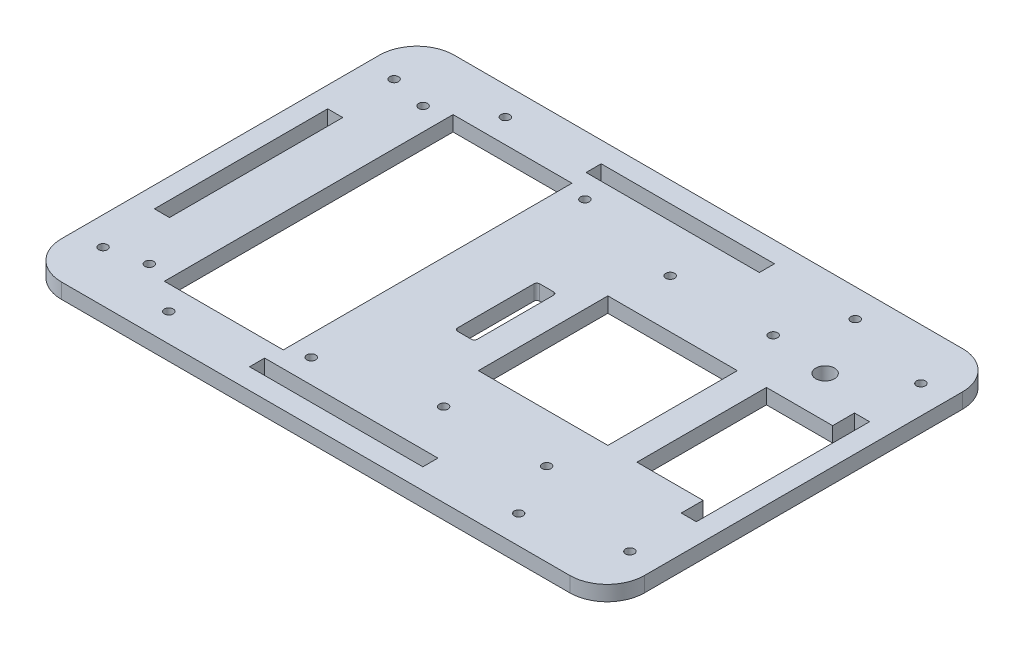
SolidWorks part; units mm, degrees
ref_plane "Front Plane" through (0, 0, 0) normal (0, 0, 1) x (1, 0, 0)
ref_plane "Top Plane" through (0, 0, 0) normal (0, 1, 0) x (1, 0, 0)
ref_plane "Right Plane" through (0, 0, 0) normal (1, 0, 0) x (0, 0, -1)
sketch "Sketch1" plane through (0, 0, 0) normal (0, 1, 0) x (1, 0, 0)
  line L1 (-55.2072, 101.2499) -> (117.5428, 101.2499)
  line L2 (-67.9072, 88.5499) -> (-67.9072, -19.5301)
  line L3 (-55.2072, -32.2301) -> (117.5428, -32.2301)
  line L4 (130.2428, 88.5499) -> (130.2428, -19.5301)
  arc A0 (-55.2072, -32.2301) -> (-67.9072, -19.5301) centre (-55.2072, -19.5301) cw
  arc A1 (-55.2072, 101.2499) -> (-67.9072, 88.5499) centre (-55.2072, 88.5499) ccw
  arc A2 (117.5428, 101.2499) -> (130.2428, 88.5499) centre (117.5428, 88.5499) cw
  arc A3 (130.2428, -19.5301) -> (117.5428, -32.2301) centre (117.5428, -19.5301) cw
  point P6 (-67.9072, -32.2301)
  point P9 (-67.9072, 101.2499)
  point P14 (130.2428, -32.2301)
  dimension "D3" = 12.7
  dimension "D4" = 12.7
  dimension "D5" = 12.7
  dimension "D1" = 133.48
  dimension "D2" = 198.15
extrude "Main" add sketch "Sketch1" along normal blind 5.13
sketch "Sketch2" plane through (0, 5.13, 0) normal (0, 1, 0) x (1, 0, 0)
  line L0 (117.5428, 101.2499) -> (-55.2072, 101.2499) construction
  line L1 (-60.9072, 63.9499) -> (-55.7772, 63.9499)
  line L2 (-60.9072, 63.9499) -> (-60.9072, 5.0699)
  line L3 (-60.9072, 5.0699) -> (-55.7772, 5.0699)
  line L4 (-55.7772, 63.9499) -> (-55.7772, 5.0699)
  line L5 (31.1678, 101.2499) -> (31.1678, -32.2301) construction
  line L6 (-55.2072, -32.2301) -> (117.5428, -32.2301) construction
  line L7 (130.2428, 34.5099) -> (-67.9072, 34.5099) construction
  line L8 (130.2428, -19.5301) -> (130.2428, 88.5499) construction
  line L9 (1.7278, 94.2499) -> (60.6078, 94.2499)
  line L10 (1.7278, 94.2499) -> (1.7278, 89.1199)
  line L11 (1.7278, 89.1199) -> (60.6078, 89.1199)
  line L12 (60.6078, 94.2499) -> (60.6078, 89.1199)
  line L13 (123.2428, 63.9499) -> (118.1128, 63.9499)
  line L14 (123.2428, 63.9499) -> (123.2428, 5.0699)
  line L15 (118.1128, 63.9499) -> (118.1128, 5.0699)
  line L16 (123.2428, 5.0699) -> (118.1128, 5.0699)
  line L17 (-67.9072, 88.5499) -> (-67.9072, -19.5301) construction
  line L18 (60.6078, -25.2301) -> (60.6078, -20.1001)
  line L19 (1.7278, -25.2301) -> (1.7278, -20.1001)
  line L20 (1.7278, -25.2301) -> (60.6078, -25.2301)
  line L21 (1.7278, -20.1001) -> (60.6078, -20.1001)
  line L23 (-67.9072, 88.5499) -> (-67.9072, -19.5301) construction
  circle A0 centre (-28.2722, 91.6899) radius 1.5
  circle A1 centre (90.6078, 91.6899) radius 1.5
  circle A2 centre (-58.3472, -14.9301) radius 1.5
  circle A3 centre (-58.3472, 83.9499) radius 1.5
  circle A4 centre (120.6828, 83.9499) radius 1.5
  circle A5 centre (120.6828, -14.9301) radius 1.5
  circle A6 centre (90.6078, -22.6701) radius 1.5
  circle A7 centre (-28.2722, -22.6701) radius 1.5
  point P44 (31.1678, 94.2499)
  dimension "D13" = 3
  dimension "D14" = 3
  dimension "D15" = 3
  dimension "D16" = 3
  dimension "D1" = 58.88
  dimension "D2" = 5.13
  dimension "D3" = 7
  dimension "D4" = 5.13
  dimension "D5" = 37.3
  dimension "D6" = 99.075
  dimension "D7" = 58.88
  dimension "D8" = 7
  dimension "D9" = 30
  dimension "D10" = 20
  dimension "D11" = 20
  dimension "D12" = 30
  dimension "D17" = 9.56
  dimension "D18" = 9.56
  dimension "D19" = 9.56
  dimension "D20" = 9.56
extrude "Assembly slots" cut sketch "Sketch2" against normal up to next
sketch "Sketch3" plane through (0, 0, 0) normal (0, -1, 0) x (1, 0, 0)
  line L0 (117.5428, -101.2499) -> (-55.2072, -101.2499) construction
  line L1 (-37.9072, 14.5401) -> (2.4928, 14.5401)
  line L2 (-37.9072, 14.5401) -> (-37.9072, -83.5599)
  line L3 (-37.9072, -83.5599) -> (2.4928, -83.5599)
  line L4 (2.4928, 14.5401) -> (2.4928, -83.5599)
  line L5 (-67.9072, -88.5499) -> (-67.9072, 19.5301) construction
  line L6 (130.2428, 19.5301) -> (130.2428, -88.5499) construction
  line L7 (41.7428, -12.5099) -> (85.7428, -12.5099)
  line L8 (41.7428, -12.5099) -> (41.7428, -56.5099)
  line L9 (41.7428, -56.5099) -> (85.7428, -56.5099)
  line L10 (85.7428, -12.5099) -> (85.7428, -56.5099)
  dimension "D1" = 40.4
  dimension "D2" = 98.1
  dimension "D3" = 17.69
  dimension "D4" = 30
  dimension "D5" = 44
  dimension "D6" = 44
  dimension "D7" = 44.5
  dimension "D8" = 44.74
extrude "LCD and Block slot" cut sketch "Sketch3" against normal up to next
ref_plane "Plane1" through (-55.2072, 0, -101.2499) normal (-1, 0, 0) x (0, 0, 1)
hole_wizard "LCD screwholes" positions "Sketch7" profile "Sketch6" hole size "Ø3.0" standard "Ansi Metric"
sketch "Sketch7" plane through (0, 5.13, 0) normal (0, 1, 0) x (-1, 0, 0)
  line L0 (55.2072, 32.2301) -> (-117.5428, 32.2301) construction
  point P3 (45.5572, 11.9901)
  point P30 (-9.4428, 11.9901)
  point P31 (45.5572, -81.0099)
  point P32 (-9.4428, -81.0099)
  dimension "D1" = 2
  dimension "D3" = 93
  dimension "D4" = 20.24
  dimension "D2" = 2
sketch "Sketch6" plane through (-45.5572, 5.13, 11.9901) normal (1, 0, 0) x (0, 0, 1)
  line L0 (0, 0) -> (0, 26.3013)
  line L1 (0, 26.3013) -> (1.5, 25.4)
  line L2 (1.5, 25.4) -> (1.5, 0)
  line L5 (1.5, 0) -> (0, 0)
  line L10 (0, 26.3013) -> (-1.5, 25.4) construction
  line L11 (0, -6.35) -> (0, 107.95) construction
  dimension "Hole Dia." = 3
  dimension "Hole Depth" = 25.4
  dimension "Drill Angle" = 118
hole_wizard "Core screwholes" positions "Sketch9" profile "Sketch8" hole size "Ø3.0" standard "Ansi Metric"
sketch "Sketch9" plane through (0, 5.13, 0) normal (0, 1, 0) x (-1, 0, 0)
  line L0 (-117.5428, -101.2499) -> (55.2072, -101.2499) construction
  point P1 (-46.4274, -73.0099)
  dimension "D2" = 28.24
sketch "Sketch8" plane through (46.4274, 5.13, -73.0099) normal (1, 0, 0) x (0, 0, 1)
  line L0 (0, 0) -> (0, 26.3013)
  line L1 (0, 26.3013) -> (1.5, 25.4)
  line L2 (1.5, 25.4) -> (1.5, 0)
  line L5 (1.5, 0) -> (0, 0)
  line L10 (0, 26.3013) -> (-1.5, 25.4) construction
  line L11 (0, -6.35) -> (0, 107.95) construction
  dimension "Hole Dia." = 3
  dimension "Hole Depth" = 25.4
  dimension "Drill Angle" = 118
pattern_linear "Core screwholes pattern" count 2 spacing 35 along (1, 0, 0) count 2 spacing 77 along (0, 0, 1) of "Core screwholes"
sketch "Sketch11" plane through (0, 5.13, 0) normal (0, 1, 0) x (1, 0, 0)
  line L0 (117.5428, 101.2499) -> (-55.2072, 101.2499) construction
  line L1 (95.6244, 12.5099) -> (118.1244, 12.5099)
  line L2 (95.6244, 12.5099) -> (95.6244, 56.5099)
  line L3 (95.6244, 56.5099) -> (118.1244, 56.5099)
  line L4 (118.1244, 12.5099) -> (118.1244, 56.5099)
  dimension "D1" = 22.5
  dimension "D2" = 44
  dimension "D3" = 44.74
extrude "Hinge slot" cut sketch "Sketch11" against normal up to next
sketch "Sketch13" plane through (0, 5.13, 0) normal (0, 1, 0) x (1, 0, 0)
  line L1 (26.6266, 48.4799) -> (31.3266, 48.4799)
  line L2 (25.6266, 47.4799) -> (25.6266, 21.5399)
  line L3 (26.6266, 20.5399) -> (31.3266, 20.5399)
  line L4 (32.3266, 47.4799) -> (32.3266, 21.5399)
  line L5 (117.5428, 101.2499) -> (-55.2072, 101.2499) construction
  arc A0 (26.6266, 20.5399) -> (25.6266, 21.5399) centre (26.6266, 21.5399) cw
  arc A1 (32.3266, 21.5399) -> (31.3266, 20.5399) centre (31.3266, 21.5399) cw
  arc A2 (31.3266, 48.4799) -> (32.3266, 47.4799) centre (31.3266, 47.4799) cw
  arc A3 (26.6266, 48.4799) -> (25.6266, 47.4799) centre (26.6266, 47.4799) ccw
  point P10 (25.6266, 20.5399)
  point P17 (25.6266, 48.4799)
  dimension "D3" = 1
  dimension "D1" = 27.94
  dimension "D2" = 52.77
  dimension "D4" = 6.7
extrude "Latch Slot" cut sketch "Sketch13" against normal up to next
hole_wizard "Lid thermistor hole" positions "Sketch15" profile "Sketch14" hole size "#6" standard "Ansi Inch"
sketch "Sketch15" plane through (0, 5.13, 0) normal (0, 1, 0) x (-1, 0, 0)
  point P0 (-101.4724, -70.6026)
sketch "Sketch14" plane through (101.4724, 5.13, -70.6026) normal (1, 0, 0) x (0, 0, 1)
  line L0 (0, 0) -> (0, 9.5077)
  line L1 (0, 9.5077) -> (3.175, 7.6)
  line L2 (3.175, 7.6) -> (3.175, 0)
  line L5 (3.175, 0) -> (0, 0)
  line L10 (0, 9.5077) -> (-3.175, 7.6) construction
  line L11 (0, -6.35) -> (0, 107.95) construction
  dimension "Hole Dia." = 6.35
  dimension "Hole Depth" = 7.6
  dimension "Drill Angle" = 118
equation "\"D3@Sketch3\" = (\"D1@Sketch1\"-\"D2@Sketch3\")/2"
equation "\"D3@Sketch11\" = (\"D1@Sketch1\"-\"D2@Sketch11\")/2"
equation "\"D2@Sketch13\" = (\"D1@Sketch1\"-\"D1@Sketch13\")/2"
equation "\"D2@Sketch9\" = (\"D1@Sketch1\"-\"RD2@Annotations\")/2"
equation "\"D6@Sketch2\" = \"D2@Sketch1\"/2"
equation "\"D4@Sketch7\" = (\"D1@Sketch1\"-\"D3@Sketch7\")/2"
